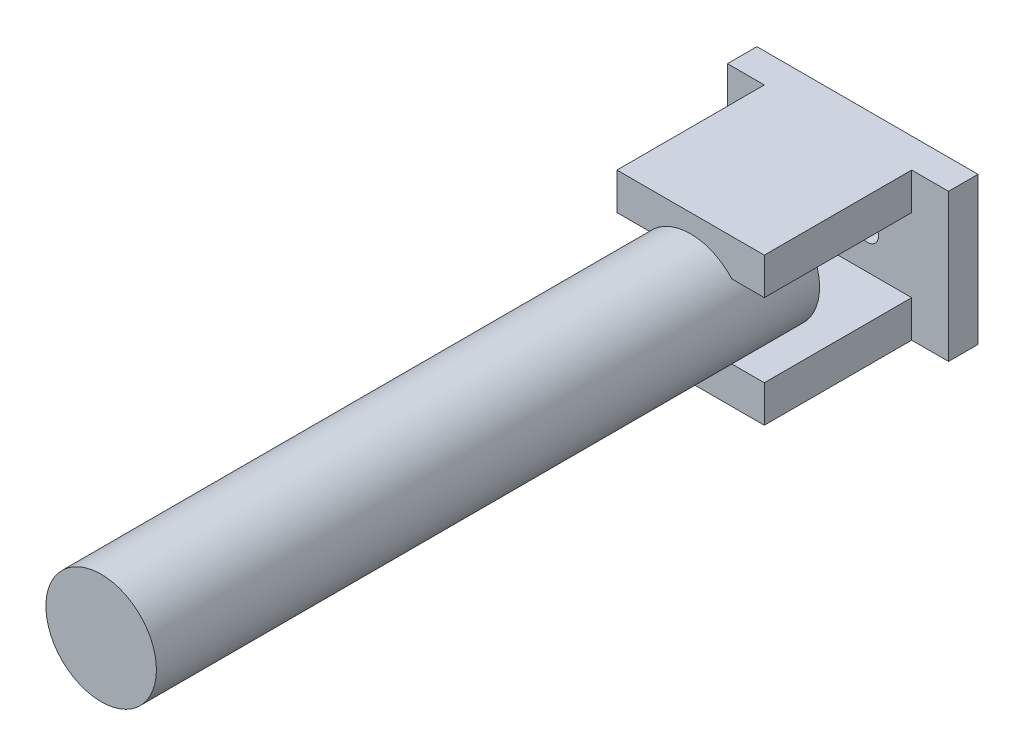
SolidWorks part; units mm, degrees
ref_plane "前视基准面" through (0, 0, 0) normal (0, 0, 1) x (1, 0, 0)
ref_plane "上视基准面" through (0, 0, 0) normal (0, 1, 0) x (1, 0, 0)
ref_plane "右视基准面" through (0, 0, 0) normal (1, 0, 0) x (0, 0, -1)
sketch "草图1" plane through (0, 0, 0) normal (0, 0, 1) x (1, 0, 0)
  line L1 (-2.9029, 3.1943) -> (5.0971, 3.1943)
  line L2 (-2.9029, 3.1943) -> (-2.9029, -1.8057)
  line L3 (-2.9029, -1.8057) -> (5.0971, -1.8057)
  line L4 (5.0971, 3.1943) -> (5.0971, -1.8057)
  line L5 (-13.9029, 10.6943) -> (16.0971, 10.6943)
  line L6 (-13.9029, 10.6943) -> (-13.9029, -9.3057)
  line L7 (-13.9029, -9.3057) -> (16.0971, -9.3057)
  line L8 (16.0971, 10.6943) -> (16.0971, -9.3057)
  line L9 (-13.9029, 10.6943) -> (16.0971, -9.3057) construction
  line L10 (-13.9029, -9.3057) -> (16.0971, 10.6943) construction
  circle A0 centre (-2.9029, 0.6943) radius 1.5
  circle A1 centre (5.0971, 0.6943) radius 1.5
  point P8 (1.0971, 0.6943)
  point P13 (0, 0)
  dimension "D3" = 20
  dimension "D1" = 8
  dimension "D2" = 5
  dimension "D4" = 30
extrude "凸台-拉伸1" add sketch "草图1" along normal blind 4 contours L8 L5 L6 L7 A1 L4 L3 L2 A0 L1 | A1 L4 L1 L2 A0 L3
sketch "草图2" plane through (0, 0, 4) normal (0, 0, 1) x (1, 0, 0)
  line L0 (-13.9029, -9.3057) -> (16.0971, -9.3057) construction
  line L1 (-13.9029, 10.6943) -> (-8.9029, 10.6943)
  line L2 (-13.9029, 10.6943) -> (-13.9029, -9.3057)
  line L3 (-13.9029, -9.3057) -> (-8.9029, -9.3057)
  line L4 (-8.9029, 10.6943) -> (-8.9029, -9.3057)
  line L5 (-8.9029, 5.6943) -> (11.0971, 5.6943)
  line L6 (16.0971, 10.6943) -> (11.0971, 10.6943)
  line L7 (16.0971, 10.6943) -> (16.0971, -9.3057)
  line L8 (16.0971, -9.3057) -> (11.0971, -9.3057)
  line L9 (11.0971, 10.6943) -> (11.0971, -9.3057)
  line L11 (-8.9029, -3.243) -> (-8.9029, 4.6315)
  line L13 (11.0971, -3.243) -> (11.0971, 4.6315)
  line L14 (-8.9029, -4.3057) -> (11.0971, -4.3057)
  line L16 (-13.9029, 10.6943) -> (16.0971, 10.6943) construction
  point P11 (1.0971, 0.6943)
  line M5 (16.0971, 10.6943) -> (-13.9029, 10.6943)
  line M7 (-13.9029, -9.3057) -> (16.0971, -9.3057)
  dimension "D1" = 5
  dimension "D2" = 5
  dimension "D3" = 5
  dimension "D4" = 5
extrude "凸台-拉伸2" add sketch "草图2" along normal blind 20 contours L9 L4 L5 M5 | L14 L4 L9 M7
sketch "草图3" plane through (0, 0, 24) normal (0, 0, 1) x (1, 0, 0)
  circle A0 centre (1.0971, 0.6943) radius 7.5
  dimension "D1" = 15
extrude "凸台-拉伸3" add sketch "草图3" along normal blind 80 and the other way blind 10
